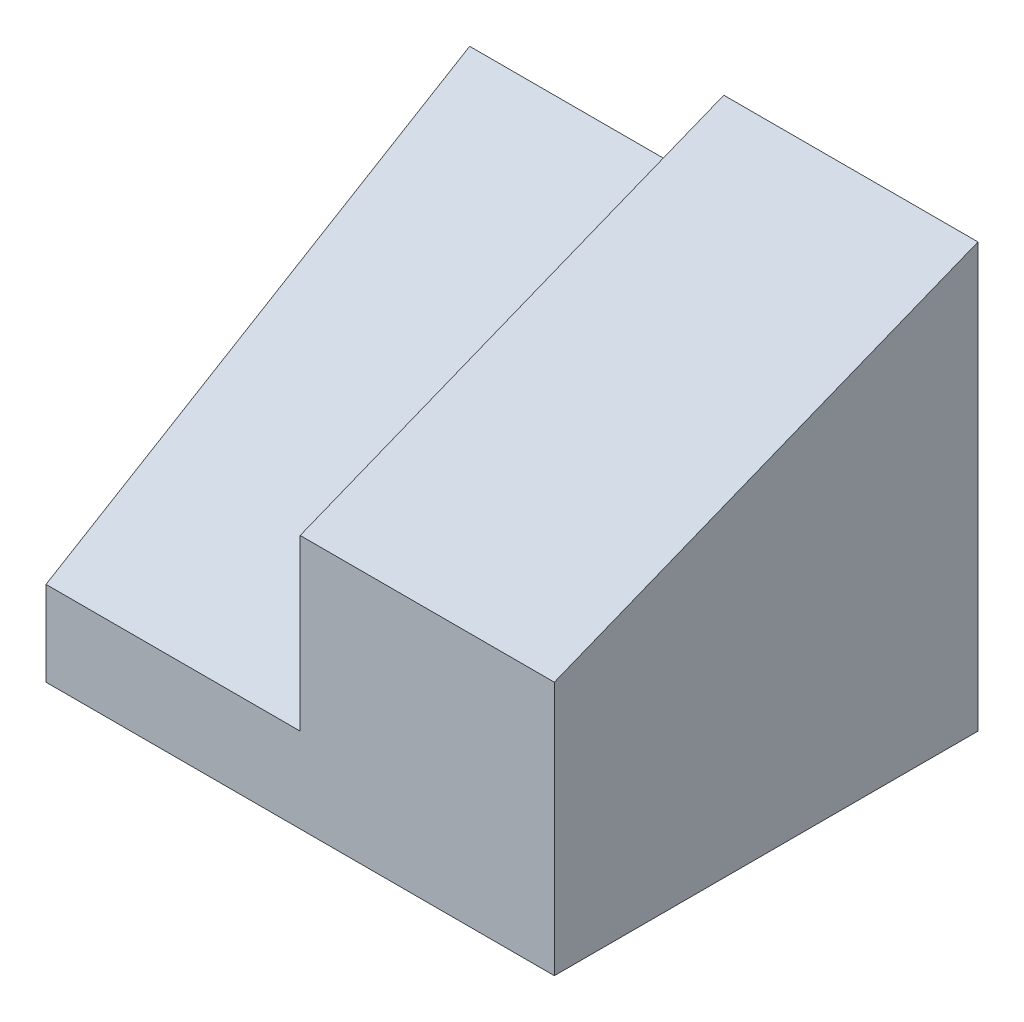
SolidWorks part; units mm, degrees
ref_plane "Front Plane" through (0, 0, 0) normal (0, 0, 1) x (1, 0, 0)
ref_plane "Top Plane" through (0, 0, 0) normal (0, 1, 0) x (1, 0, 0)
ref_plane "Right Plane" through (0, 0, 0) normal (1, 0, 0) x (0, 0, -1)
sketch "Sketch1" plane through (0, 0, 0) normal (0, 0, 1) x (1, 0, 0)
  line L0 (-30, 5) -> (-15, 5)
  line L1 (-15, 5) -> (-15, 15)
  line L2 (-15, 15) -> (0, 15)
  line L3 (0, 15) -> (0, 0)
  line L4 (0, 0) -> (-30, 0)
  line L5 (-30, 0) -> (-30, 5)
  dimension "D1" = 5
  dimension "D2" = 15
  dimension "D3" = 10
  dimension "D4" = 30
extrude "Boss-Extrude1" add sketch "Sketch1" along normal blind 25
sketch "Sketch2" plane through (0, 0, 0) normal (1, 0, 0) x (0, 0, -1)
  line L0 (0, 15) -> (0, 25)
  line L1 (0, 25) -> (-25, 15)
  line L2 (-25, 15) -> (0, 15)
  dimension "D1" = 10
extrude "Boss-Extrude2" add sketch "Sketch2" against normal blind 15
sketch "Sketch3" plane through (-15, 0, 0) normal (-1, 0, 0) x (0, 0, 1)
  line L0 (0, 5) -> (0, 20)
  line L1 (0, 25) -> (0, 5) construction
  line L2 (0, 20) -> (25, 5)
  line L3 (25, 5) -> (0, 5)
  dimension "D1" = 15
extrude "Boss-Extrude3" add sketch "Sketch3" along normal blind 15
